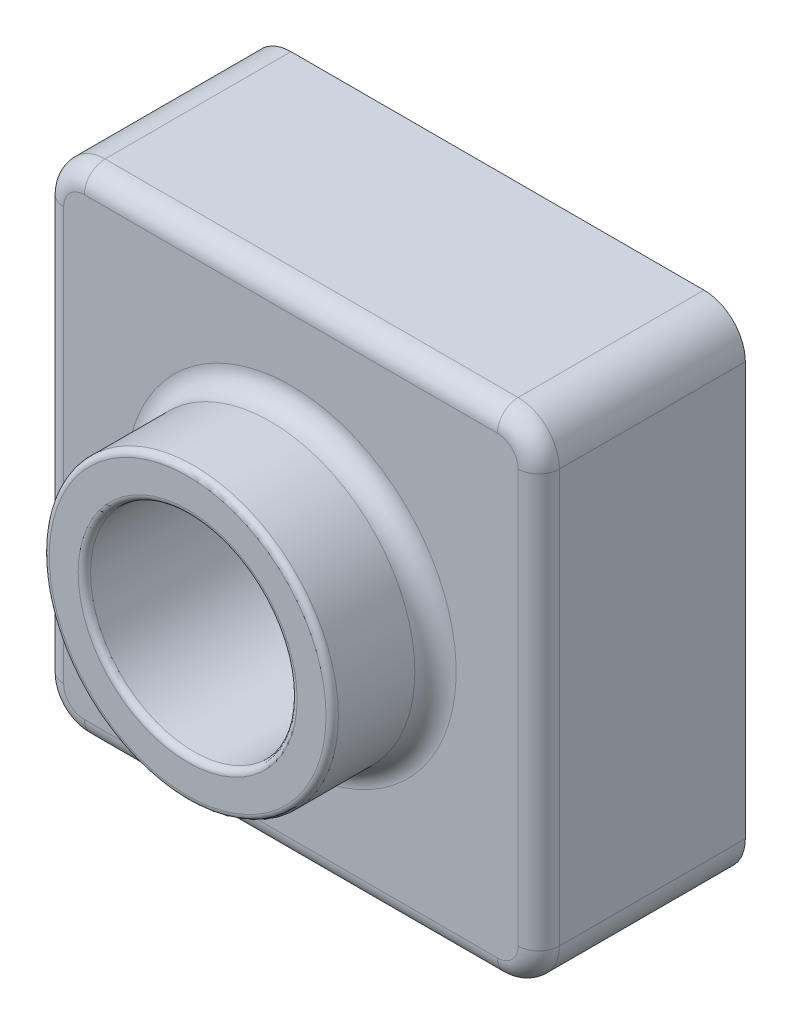
SolidWorks part; units mm, degrees
material "Cast Alloy Steel"
ref_plane "Front" through (0, 0, 0) normal (0, 0, 1) x (1, 0, 0)
ref_plane "Top" through (0, 0, 0) normal (0, 1, 0) x (1, 0, 0)
ref_plane "Right" through (0, 0, 0) normal (1, 0, 0) x (0, 0, -1)
sketch "Sketch1" plane through (0, 0, 0) normal (0, 0, 1) x (1, 0, 0)
  line L1 (0, 0) -> (120, 0)
  line L2 (0, 0) -> (0, 120)
  line L3 (0, 120) -> (120, 120)
  line L4 (120, 0) -> (120, 120)
  point P5 (143.3333, 97.5)
  point P6 (120, 79.7222)
  dimension "D1" = 120
  dimension "D2" = 120
extrude "Boss-Extrude1" add sketch "Sketch1" along normal blind 50
sketch "Sketch2" plane through (0, 0, 50) normal (0, 0, 1) x (1, 0, 0)
  line L0 (120, 120) -> (0, 120) construction
  line L1 (0, 120) -> (0, 0) construction
  circle A0 centre (60, 60) radius 35
  dimension "D1" = 70
  dimension "D2" = 60
  dimension "D3" = 60
extrude "Boss-Extrude2" add sketch "Sketch2" along normal blind 25
sketch "Sketch6" plane through (0, 0, 75) normal (0, 0, 1) x (1, 0, 0)
  circle A2 centre (60, 60) radius 25
  dimension "D1" = 50
extrude "Cut-Extrude1" cut sketch "Sketch6" against normal through all
fillet "Fillet1" radius 10 4 edges at (0, 0, 25) (120, 0, 25) (120, 120, 25) (0, 120, 25)
fillet "Fillet2" radius 1.5 2 edges at (95, 60, 75) (85, 60, 75)
fillet "Fillet3" radius 5 9 edges at (2.9289, 117.0711, 50) (60, 120, 50) (117.0711, 117.0711, 50) (120, 60, 50) (117.0711, 2.9289, 50) (60, 0, 50) (2.9289, 2.9289, 50) (0, 60, 50) (95, 60, 50)
shell "Shell1" thickness 2
